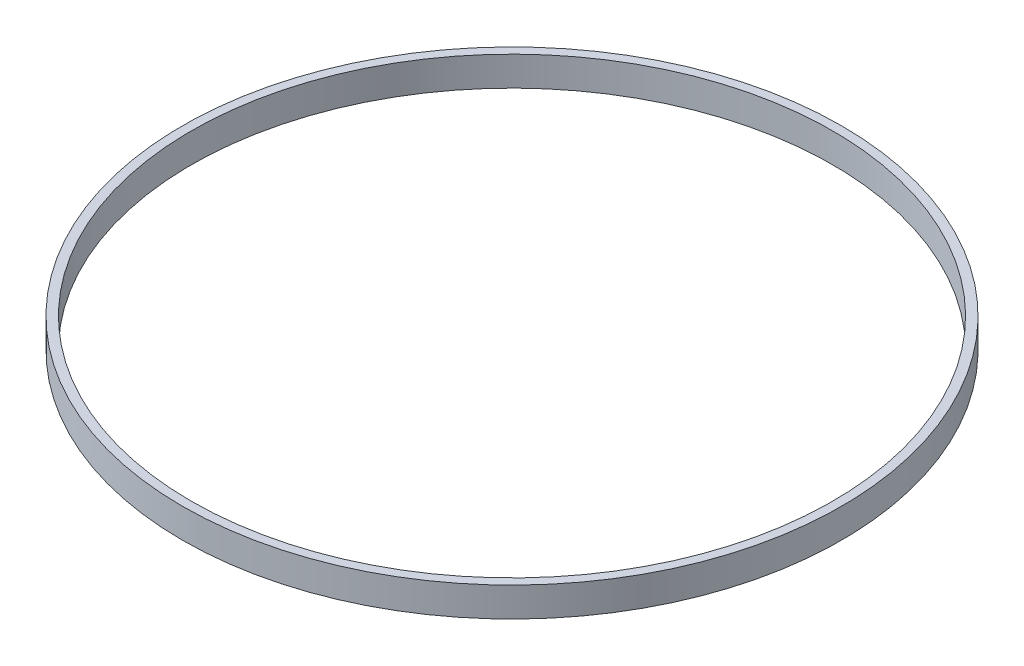
SolidWorks part; units mm, degrees
ref_plane "Front Plane" through (0, 0, 0) normal (0, 0, 1) x (1, 0, 0)
ref_plane "Top Plane" through (0, 0, 0) normal (0, 1, 0) x (1, 0, 0)
ref_plane "Right Plane" through (0, 0, 0) normal (1, 0, 0) x (0, 0, -1)
sketch "Sketch1" plane through (0, 0, 0) normal (0, 1, 0) x (1, 0, 0)
  circle A0 centre (0, 0) radius 28
  circle A1 centre (0, 0) radius 27.25
  dimension "D1" = 56
  dimension "D2" = 54.5
extrude "Boss-Extrude1" add sketch "Sketch1" along normal blind 2.5
